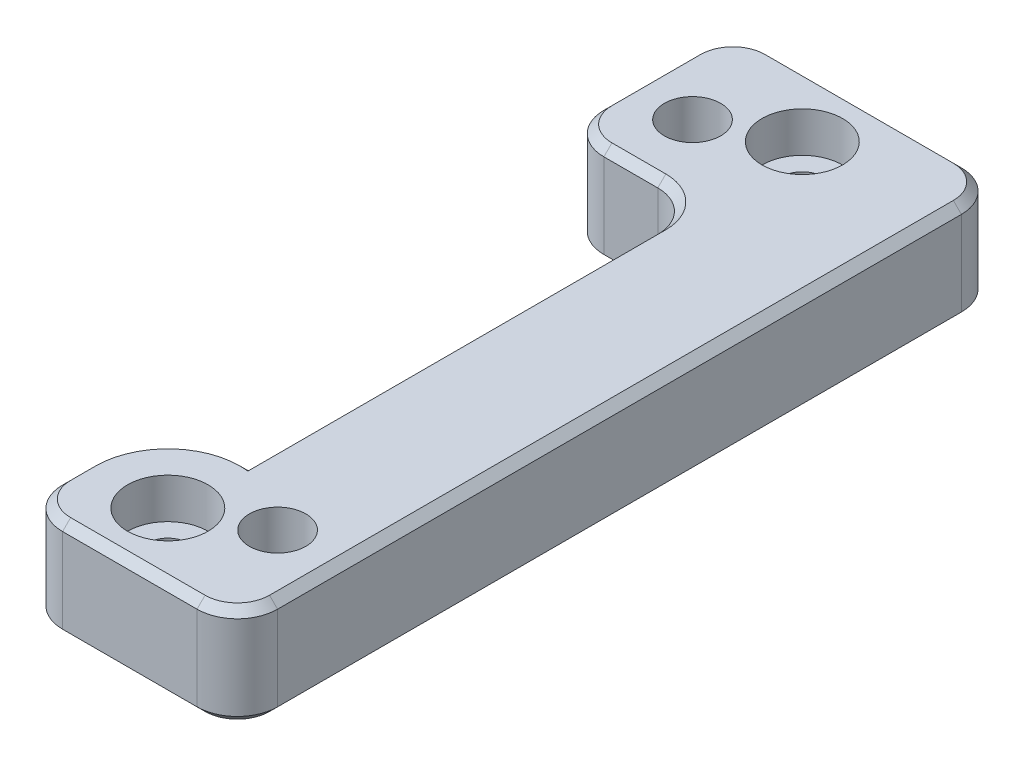
SolidWorks part; units mm, degrees
ref_plane "Front Plane" through (0, 0, 0) normal (0, 0, 1) x (1, 0, 0)
ref_plane "Top Plane" through (0, 0, 0) normal (0, 1, 0) x (1, 0, 0)
ref_plane "Right Plane" through (0, 0, 0) normal (1, 0, 0) x (0, 0, -1)
sketch "Sketch2" plane through (0, 0, 0) normal (0, 1, 0) x (1, 0, 0)
  line L0 (-6.675, -18.975) -> (6.675, 18.975) construction
  line L1 (-6.675, 18.975) -> (6.675, 18.975)
  line L2 (-6.675, 18.975) -> (-6.675, -18.975)
  line L3 (-6.675, -18.975) -> (6.675, -18.975)
  line L4 (6.675, 18.975) -> (6.675, -18.975)
  line L5 (0, -15.75) -> (0, 15.75) construction
  circle A0 centre (-3.675, 13.975) radius 1.4
  circle A1 centre (3.675, -13.975) radius 1.4
  circle A2 centre (0, 15.75) radius 1
  circle A3 centre (0, -15.75) radius 1
  point P8 (0, 0)
  point P14 (0, 13.975)
  point P15 (0, 0)
  dimension "D1" = 2.8
  dimension "D2" = 2.8
  dimension "D10" = 2
  dimension "D11" = 2
  dimension "D3" = 7.35
  dimension "D4" = 27.95
  dimension "D5" = 5
  dimension "D6" = 3
  dimension "D7" = 3
  dimension "D8" = 5
  dimension "D9" = 31.5
extrude "Boss-Extrude1" add sketch "Sketch2" along normal blind 5
sketch "Sketch3" plane through (0, 5, 0) normal (0, 1, 0) x (1, 0, 0)
  circle A0 centre (0, 15.75) radius 2
  circle A1 centre (0, -15.75) radius 2
  dimension "D1" = 4
  dimension "D2" = 4
extrude "Cut-Extrude1" cut sketch "Sketch3" against normal blind 2
sketch "Sketch4" plane through (0, 5, 0) normal (0, 1, 0) x (1, 0, 0)
  line L0 (-6.675, 10.575) -> (-2, 10.575)
  line L1 (-6.675, 18.975) -> (-6.675, -18.975) construction
  line L2 (0, 8.575) -> (0, -11.75)
  line L3 (-4, -15.75) -> (-4, -18.975)
  line L4 (-6.675, -18.975) -> (6.675, -18.975) construction
  line L5 (-6.675, 10.575) -> (-6.675, -18.975)
  line L6 (-6.675, -18.975) -> (-4, -18.975)
  line L7 (-6.675, 12.575) -> (6.675, 12.575) construction
  line L8 (6.675, -18.975) -> (6.675, 18.975) construction
  arc A0 (-2, 10.575) -> (0, 8.575) centre (-2, 8.575) cw
  arc A1 (0, -11.75) -> (-4, -15.75) centre (0, -15.75) ccw
  circle A2 centre (0, -15.75) radius 1 construction
  circle A3 centre (0, -15.75) radius 2 construction
  circle A4 centre (-3.675, 13.975) radius 1.4 construction
  point P18 (6.675, 12.6475)
  dimension "D1" = 2
  dimension "D3" = 2
  dimension "D2" = 2
extrude "Cut-Extrude2" cut sketch "Sketch4" against normal through all
fillet "Fillet1" radius 2 5 edges at (-6.675, 2.5, -10.575) (-6.675, 2.5, -18.975) (6.675, 2.5, -18.975) (6.675, 2.5, 18.975) (-4, 2.5, 18.975)
chamfer "Chamfer1" distance 0.4 angle 45 28 edges at (-2.8284, 0, 12.9216) (-4, 0, 16.3625) (-3.4142, 0, 18.3892) (1.3375, 0, 18.975) (6.0892, 0, 18.3892) (6.675, 0, 0) (6.0892, 0, -18.3892) (0, 0, -18.975) (-6.0892, 0, -18.3892) (0, 0, 1.5875) (-6.675, 0, -14.775) (-0.5858, 0, -9.9892) (-6.0892, 0, -11.1608) (-3.3375, 0, -10.575) (-2.8284, 5, 12.9216) (-4, 5, 16.3625) (-3.4142, 5, 18.3892) (1.3375, 5, 18.975) (6.0892, 5, 18.3892) (6.675, 5, 0) (6.0892, 5, -18.3892) (0, 5, -18.975) (-6.0892, 5, -18.3892) (0, 5, 1.5875) (-6.675, 5, -14.775) (-0.5858, 5, -9.9892) (-6.0892, 5, -11.1608) (-3.3375, 5, -10.575)
